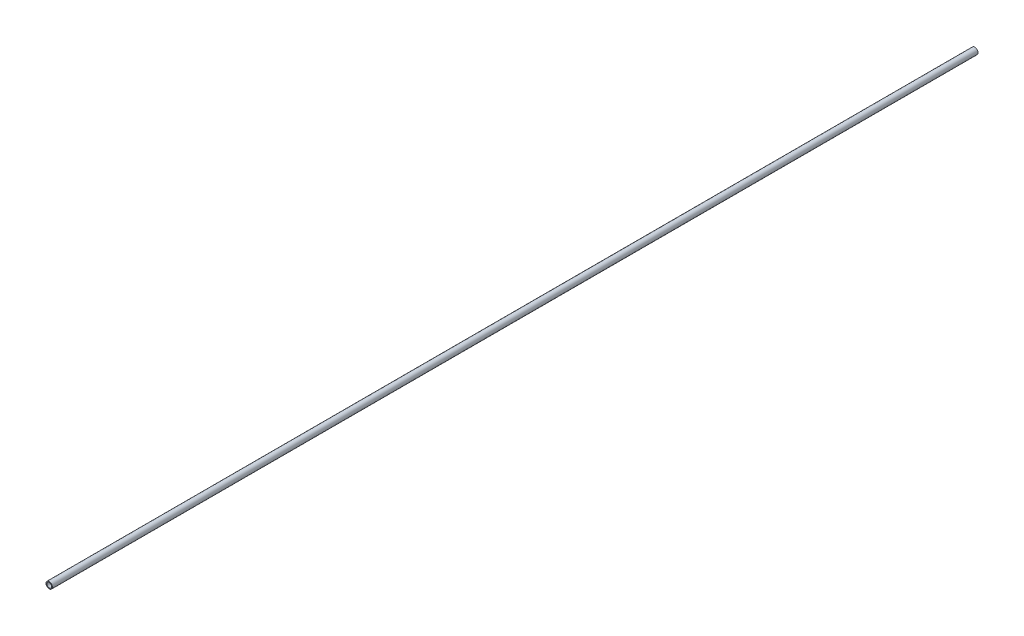
SolidWorks part; units mm, degrees
material "6063-O, Extruded Rod (SS)"
ref_plane "Front Plane" through (0, 0, 0) normal (0, 0, 1) x (1, 0, 0)
ref_plane "Top Plane" through (0, 0, 0) normal (0, 1, 0) x (1, 0, 0)
ref_plane "Right Plane" through (0, 0, 0) normal (1, 0, 0) x (0, 0, -1)
sketch "Sketch1" plane through (0, 0, 0) normal (0, 0, 1) x (1, 0, 0)
  circle A0 centre (0, 0) radius 6.35
  circle A1 centre (0, 0) radius 4.699
  dimension "D1" = 12.7
  dimension "D2" = 1.651
extrude "Boss-Extrude1" add sketch "Sketch1" along normal blind 1828.8
